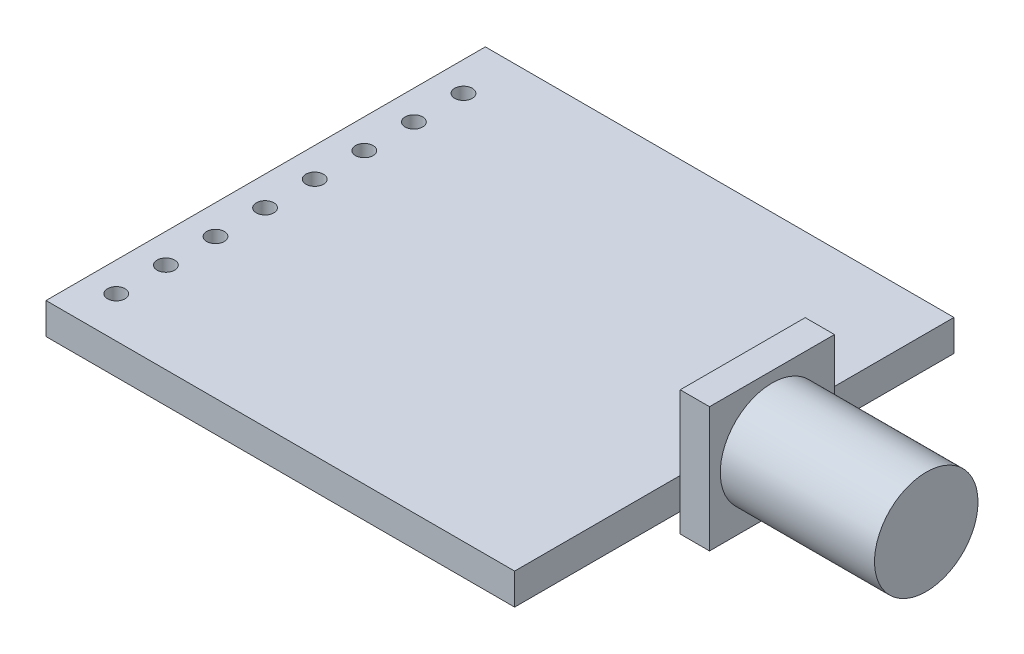
SolidWorks part; units mm, degrees
ref_plane "Front Plane" through (0, 0, 0) normal (0, 0, 1) x (1, 0, 0)
ref_plane "Top Plane" through (0, 0, 0) normal (0, 1, 0) x (1, 0, 0)
ref_plane "Right Plane" through (0, 0, 0) normal (1, 0, 0) x (0, 0, -1)
sketch "Sketch1" plane through (0, 0, 0) normal (0, 1, 0) x (1, 0, 0)
  line L1 (-12, 11.25) -> (12, 11.25)
  line L2 (-12, 11.25) -> (-12, -11.25)
  line L3 (-12, -11.25) -> (12, -11.25)
  line L4 (12, 11.25) -> (12, -11.25)
  line L5 (-12, 11.25) -> (12, -11.25) construction
  line L6 (-12, -11.25) -> (12, 11.25) construction
  point P0 (0, 0)
  dimension "D1" = 22.5
  dimension "D2" = 24
extrude "Boss-Extrude1" add sketch "Sketch1" along normal blind 1.6
sketch "Sketch2" plane through (12, 0, 0) normal (1, 0, 0) x (0, 0, -1)
  line L0 (0.431, 0) -> (0.431, 7.5289) construction
  line L1 (-11.25, 0) -> (11.25, 0) construction
  line L3 (-2.769, 5.4) -> (3.631, 5.4)
  line L4 (-2.769, 5.4) -> (-2.769, -1)
  line L5 (-2.769, -1) -> (3.631, -1)
  line L6 (3.631, 5.4) -> (3.631, -1)
  line L7 (-2.769, 5.4) -> (3.631, -1) construction
  line L8 (-2.769, -1) -> (3.631, 5.4) construction
  point P4 (0.431, 2.2)
  dimension "D1" = 6.4
  dimension "D2" = 6.4
  dimension "D3" = 1
extrude "Boss-Extrude2" add sketch "Sketch2" along normal blind 1.5
sketch "Sketch3" plane through (13.5, 0, 0) normal (1, 0, 0) x (0, 0, -1)
  line L0 (0.431, 5.4) -> (0.431, -1) construction
  line L1 (3.631, 5.4) -> (-2.769, 5.4) construction
  line L2 (-2.769, -1) -> (3.631, -1) construction
  circle A0 centre (0.431, 2.2) radius 2.65
  dimension "D1" = 5.3
extrude "Boss-Extrude3" add sketch "Sketch3" along normal blind 7.9
sketch "Sketch4" plane through (0, 1.6, 0) normal (0, 1, 0) x (1, 0, 0)
  line L0 (-12, 11.25) -> (-12, -11.25) construction
  line L2 (-12, -11.25) -> (12, -11.25) construction
  circle A0 centre (-10.5, -9.15) radius 0.45
  dimension "D2" = 0.9
  dimension "D1" = 1.5
  dimension "D3" = 2.1
extrude "Cut-Extrude1" cut sketch "Sketch4" against normal through all
pattern_linear "LPattern1" count 8 spacing 2.54 along (0, 0, -1) of "Cut-Extrude1"
